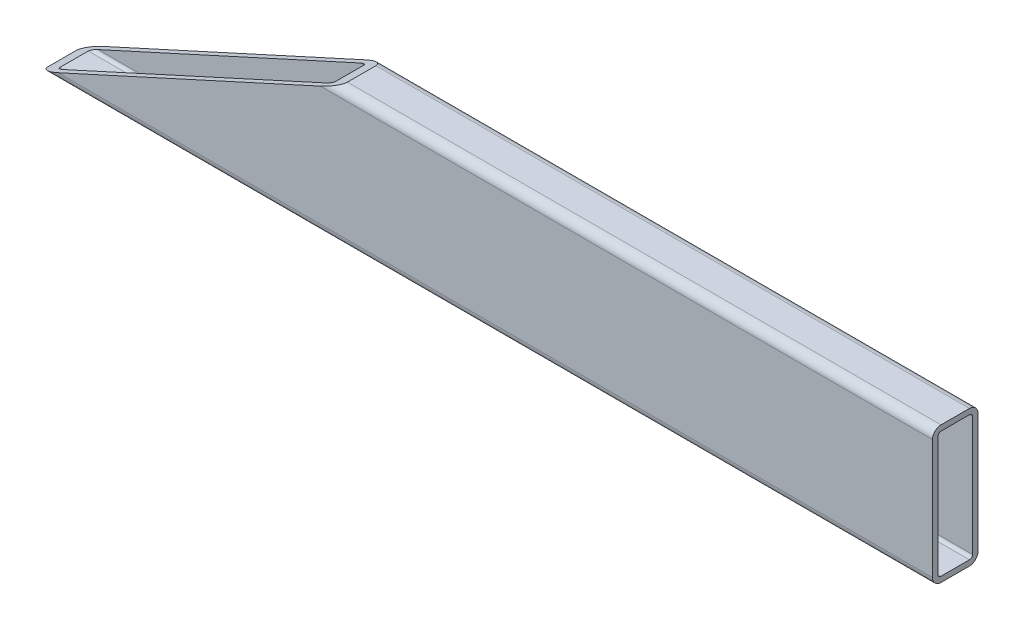
SolidWorks part; units mm, degrees
material "Plain Carbon Steel"
ref_plane "Front Plane" through (0, 0, 0) normal (0, 0, 1) x (1, 0, 0)
ref_plane "Top Plane" through (0, 0, 0) normal (0, 1, 0) x (1, 0, 0)
ref_plane "Right Plane" through (0, 0, 0) normal (1, 0, 0) x (0, 0, -1)
sketch "Sketch1" plane through (0, 0, 0) normal (0, 1, 0) x (1, 0, 0)
  line L0 (249.2375, 0) -> (-249.2375, 0)
  point P4 (0, 0)
  dimension "D1" = 498.475
other "Rectangular tube 3 X 2 X 0.25(1)"
ref_plane "Plane1" through (249.2375, 0, 0) normal (-1, 0, 0) x (0, 0, 1)
sketch "Sketch13" plane through (249.2375, 0, 0) normal (-1, 0, 0) x (0, 0, 1)
  line L0 (-7.9375, -35.052) -> (7.9375, -35.052)
  line L1 (-9.652, -33.3375) -> (-9.652, 33.3375)
  line L2 (7.9375, 35.052) -> (-7.9375, 35.052)
  line L3 (9.652, 33.3375) -> (9.652, -33.3375)
  line L4 (-7.9375, -38.1) -> (7.9375, -38.1)
  line L5 (-12.7, -33.3375) -> (-12.7, 33.3375)
  line L6 (7.9375, 38.1) -> (-7.9375, 38.1)
  line L7 (12.7, 33.3375) -> (12.7, -33.3375)
  line L8 (0, 0) -> (12.7, 0) construction
  line L9 (0, 0) -> (0, 38.1) construction
  arc A0 (12.7, 33.3375) -> (7.9375, 38.1) centre (7.9375, 33.3375) ccw
  arc A1 (7.9375, -38.1) -> (12.7, -33.3375) centre (7.9375, -33.3375) ccw
  arc A2 (-12.7, -33.3375) -> (-7.9375, -38.1) centre (-7.9375, -33.3375) ccw
  arc A3 (-7.9375, 38.1) -> (-12.7, 33.3375) centre (-7.9375, 33.3375) ccw
  arc A4 (-7.9375, 35.052) -> (-9.652, 33.3375) centre (-7.9375, 33.3375) ccw
  arc A5 (9.652, 33.3375) -> (7.9375, 35.052) centre (7.9375, 33.3375) ccw
  arc A6 (7.9375, -35.052) -> (9.652, -33.3375) centre (7.9375, -33.3375) ccw
  arc A7 (-9.652, -33.3375) -> (-7.9375, -35.052) centre (-7.9375, -33.3375) ccw
  point P3 (0, -38.1)
  point P4 (-12.7, 0)
  point P5 (0, 0)
  point P6 (12.7, -38.1)
  point P7 (-12.7, -38.1)
  point P8 (-12.7, 38.1)
  point P33 (0, 0)
  point P35 (12.7, 38.1)
  point P36 (12.7, 0)
  point P37 (0, 38.1)
  dimension "D1" = 4.7625
  dimension "Thickness" = 3.048
  dimension "V_leg" = 76.2
  dimension "H_leg" = 25.4
sketch "s" plane through (0, 0, 12.7) normal (0, 0, 1) x (1, 0, 0)
  line L0 (-249.2375, -38.1) -> (-249.2375, 38.1)
  line L3 (-249.2375, 38.1) -> (-82.0319, 38.1)
  line L4 (-82.0319, 38.1) -> (-249.2375, -38.1)
  line L16 (-249.2375, 38.1) -> (249.2375, 38.1) construction
  line L17 (-249.2375, -38.1) -> (249.2375, -38.1) construction
  dimension "D1" = 65.5
extrude "Cut-Extrude1" cut sketch "s" against normal through all
